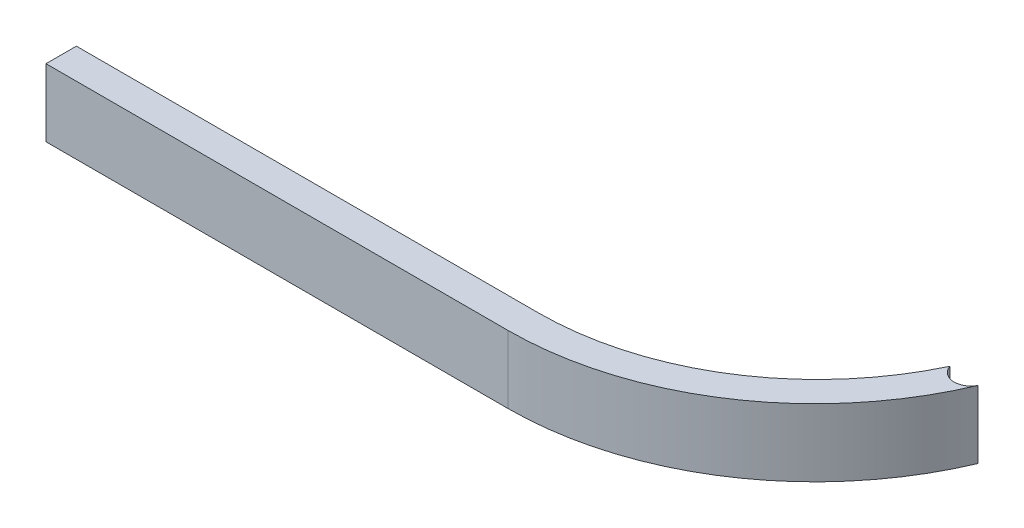
SolidWorks part; units mm, degrees
ref_plane "Front Plane" through (0, 0, 0) normal (0, 0, 1) x (1, 0, 0)
ref_plane "Top Plane" through (0, 0, 0) normal (0, 1, 0) x (1, 0, 0)
ref_plane "Right Plane" through (0, 0, 0) normal (1, 0, 0) x (0, 0, -1)
sketch "Sketch2" plane through (0, 0, 0) normal (0, 1, 0) x (1, 0, 0)
  line L0 (-53.431, -11.5617) -> (14.817, -11.5617)
  line L1 (-53.431, -7.0717) -> (14.817, -7.0717)
  line L2 (-53.431, -7.0717) -> (-53.431, -11.5617)
  arc A0 (14.817, -11.5617) -> (56.7658, 16.5008) centre (14.817, 33.8228) ccw
  arc A1 (14.817, -7.0717) -> (52.084, 16.5008) centre (14.817, 34.1732) ccw
  arc A2 (52.084, 16.5008) -> (56.7658, 16.5008) centre (54.4249, 17.2613) ccw
  dimension "D2" = 4.9227
  dimension "D1" = 4.49
extrude "Boss-Extrude1" add sketch "Sketch2" along normal blind 10 contours A2 A1 L1 L2 L0 A0
